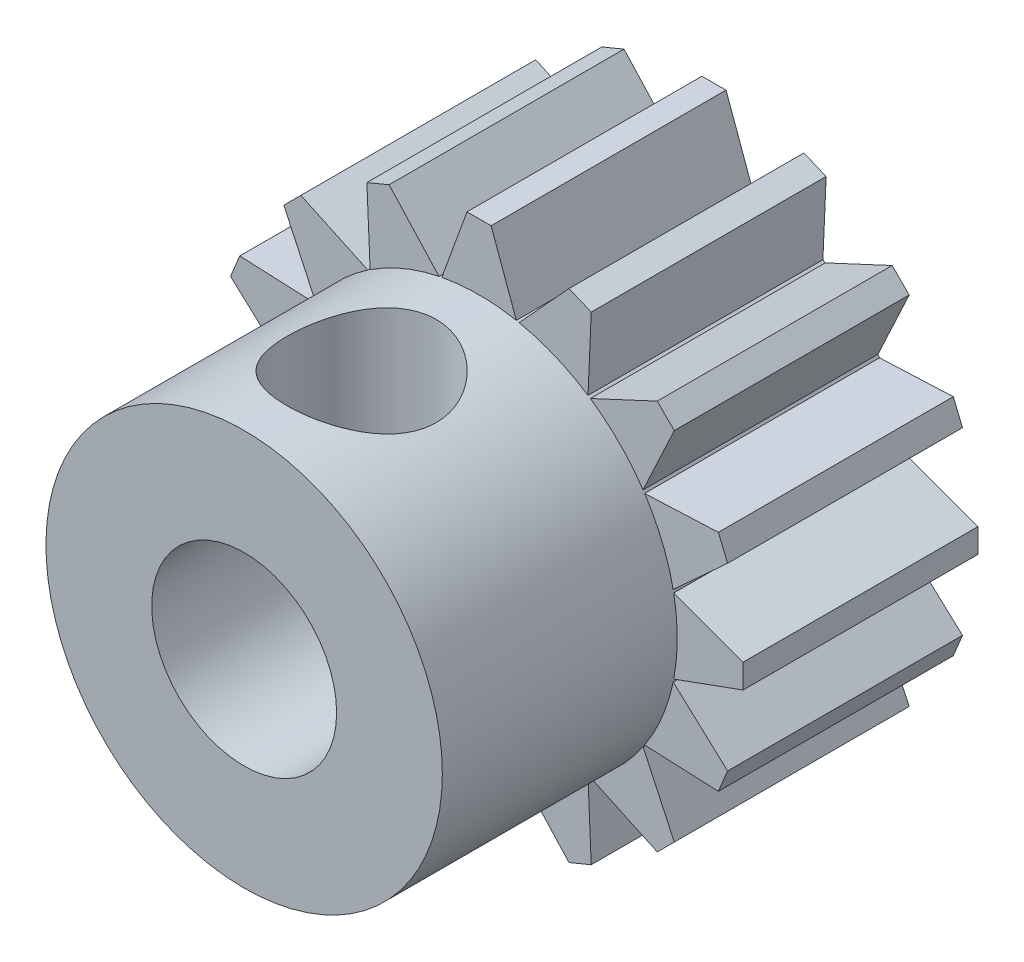
SolidWorks part; units mm, degrees
ref_plane "Front Plane" through (0, 0, 0) normal (0, 0, 1) x (1, 0, 0)
ref_plane "Top Plane" through (0, 0, 0) normal (0, 1, 0) x (1, 0, 0)
ref_plane "Right Plane" through (0, 0, 0) normal (1, 0, 0) x (0, 0, -1)
ref_plane "Plane1" through (0, 0, -3.175) normal (0, 0, -1) x (-1, 0, 0)
sketch "Sketch1" plane through (0, 0, -3.175) normal (0, 0, -1) x (-1, 0, 0)
  line L0 (-4.4757, 2.9452) -> (-6.4695, 3.0322)
  line L1 (-6.4695, 3.0322) -> (-6.7187, 2.4305)
  line L2 (-6.7187, 2.4305) -> (-5.2474, 1.0823)
  line L3 (-5.2621, 1.0082) -> (-7.1374, 0.3257)
  line L4 (-7.1374, 0.3257) -> (-7.1374, -0.3257)
  line L5 (-7.1374, -0.3257) -> (-5.2621, -1.0082)
  line L6 (-5.2474, -1.0823) -> (-6.7187, -2.4305)
  line L7 (-6.7187, -2.4305) -> (-6.4695, -3.0322)
  line L8 (-6.4695, -3.0322) -> (-4.4757, -2.9452)
  line L9 (-4.4338, -3.008) -> (-5.2772, -4.8166)
  line L10 (-5.2772, -4.8166) -> (-4.8166, -5.2772)
  line L11 (-4.8166, -5.2772) -> (-3.008, -4.4338)
  line L12 (-2.9452, -4.4757) -> (-3.0322, -6.4695)
  line L13 (-3.0322, -6.4695) -> (-2.4305, -6.7187)
  line L14 (-2.4305, -6.7187) -> (-1.0823, -5.2474)
  line L15 (-1.0082, -5.2621) -> (-0.3257, -7.1374)
  line L16 (-0.3257, -7.1374) -> (0.3257, -7.1374)
  line L17 (0.3257, -7.1374) -> (1.0082, -5.2621)
  line L18 (1.0823, -5.2474) -> (2.4305, -6.7187)
  line L19 (2.4305, -6.7187) -> (3.0322, -6.4695)
  line L20 (3.0322, -6.4695) -> (2.9452, -4.4757)
  line L21 (3.008, -4.4338) -> (4.8166, -5.2772)
  line L22 (4.8166, -5.2772) -> (5.2772, -4.8166)
  line L23 (5.2772, -4.8166) -> (4.4338, -3.008)
  line L24 (4.4757, -2.9452) -> (6.4695, -3.0322)
  line L25 (6.4695, -3.0322) -> (6.7187, -2.4305)
  line L26 (6.7187, -2.4305) -> (5.2474, -1.0823)
  line L27 (5.2621, -1.0082) -> (7.1374, -0.3257)
  line L28 (7.1374, -0.3257) -> (7.1374, 0.3257)
  line L29 (7.1374, 0.3257) -> (5.2621, 1.0082)
  line L30 (5.2474, 1.0823) -> (6.7187, 2.4305)
  line L31 (6.7187, 2.4305) -> (6.4695, 3.0322)
  line L32 (6.4695, 3.0322) -> (4.4757, 2.9452)
  line L33 (4.4338, 3.008) -> (5.2772, 4.8166)
  line L34 (5.2772, 4.8166) -> (4.8166, 5.2772)
  line L35 (4.8166, 5.2772) -> (3.008, 4.4338)
  line L36 (2.9452, 4.4757) -> (3.0322, 6.4695)
  line L37 (3.0322, 6.4695) -> (2.4305, 6.7187)
  line L38 (2.4305, 6.7187) -> (1.0823, 5.2474)
  line L39 (1.0082, 5.2621) -> (0.3257, 7.1374)
  line L40 (0.3257, 7.1374) -> (-0.3257, 7.1374)
  line L41 (-0.3257, 7.1374) -> (-1.0082, 5.2621)
  line L42 (-1.0823, 5.2474) -> (-2.4305, 6.7187)
  line L43 (-2.4305, 6.7187) -> (-3.0322, 6.4695)
  line L44 (-3.0322, 6.4695) -> (-2.9452, 4.4757)
  line L45 (-3.008, 4.4338) -> (-4.8166, 5.2772)
  line L46 (-4.8166, 5.2772) -> (-5.2772, 4.8166)
  line L47 (-5.2772, 4.8166) -> (-4.4338, 3.008)
  arc A0 (-4.4338, 3.008) -> (-4.4757, 2.9452) centre (0, 0) ccw
  arc A1 (-5.2474, 1.0823) -> (-5.2621, 1.0082) centre (0, 0) ccw
  arc A2 (-5.2621, -1.0082) -> (-5.2474, -1.0823) centre (0, 0) ccw
  arc A3 (-4.4757, -2.9452) -> (-4.4338, -3.008) centre (0, 0) ccw
  arc A4 (-3.008, -4.4338) -> (-2.9452, -4.4757) centre (0, 0) ccw
  arc A5 (-1.0823, -5.2474) -> (-1.0082, -5.2621) centre (0, 0) ccw
  arc A6 (1.0082, -5.2621) -> (1.0823, -5.2474) centre (0, 0) ccw
  arc A7 (2.9452, -4.4757) -> (3.008, -4.4338) centre (0, 0) ccw
  arc A8 (4.4338, -3.008) -> (4.4757, -2.9452) centre (0, 0) ccw
  arc A9 (5.2474, -1.0823) -> (5.2621, -1.0082) centre (0, 0) ccw
  arc A10 (5.2621, 1.0082) -> (5.2474, 1.0823) centre (0, 0) ccw
  arc A11 (4.4757, 2.9452) -> (4.4338, 3.008) centre (0, 0) ccw
  arc A12 (3.008, 4.4338) -> (2.9452, 4.4757) centre (0, 0) ccw
  arc A13 (1.0823, 5.2474) -> (1.0082, 5.2621) centre (0, 0) ccw
  arc A14 (-1.0082, 5.2621) -> (-1.0823, 5.2474) centre (0, 0) ccw
  arc A15 (-2.9452, 4.4757) -> (-3.008, 4.4338) centre (0, 0) ccw
extrude "Boss-Extrude1" add sketch "Sketch1" against normal blind 6.35
sketch "Sketch2" plane through (0, 0, 3.175) normal (0, 0, 1) x (1, 0, 0)
  circle A0 centre (0, 0) radius 5.3578
extrude "Boss-Extrude2" add sketch "Sketch2" along normal blind 6.35
hole_wizard "#10 Clearance Hole1" positions "Sketch4" profile "Sketch3" hole size "#10" standard "ANSI Inch"
sketch "Sketch4" plane through (0, 0, 9.525) normal (0, 0, 1) x (1, 0, 0)
  point P0 (0, 0)
sketch "Sketch3" plane through (0, 0, 9.525) normal (1, 0, 0) x (0, -1, 0)
  line L0 (0, 0) -> (0, 12.7)
  line L1 (0, 12.7) -> (2.5, 12.7)
  line L2 (2.5, 12.7) -> (2.5, 0)
  line L5 (2.5, 0) -> (0, 0)
  line L11 (0, -6.35) -> (0, 107.95) construction
  dimension "Thru Hole Dia." = 5
  dimension "Thru Hole Depth" = 12.7
ref_plane "Plane2" through (0, 1.4739, 0) normal (0, -1, 0) x (-1, 0, 0)
hole_wizard "#21 (0.159) Diameter Hole1" positions "Sketch6" profile "Sketch5" hole size "#21" standard "ANSI Inch"
sketch "Sketch6" plane through (0, 1.4739, 0) normal (0, -1, 0) x (-1, 0, 0)
  point P0 (0, -6.35)
sketch "Sketch5" plane through (0, 1.4739, 6.35) normal (1, 0, 0) x (0, 0, -1)
  line L0 (0, 0) -> (0, 5.6635)
  line L1 (0, 5.6635) -> (2.0193, 5.6635)
  line L2 (2.0193, 5.6635) -> (2.0193, 0)
  line L5 (2.0193, 0) -> (0, 0)
  line L11 (0, -6.35) -> (0, 107.95) construction
  dimension "Thru Hole Dia." = 4.0386
  dimension "Thru Hole Depth" = 5.6635
